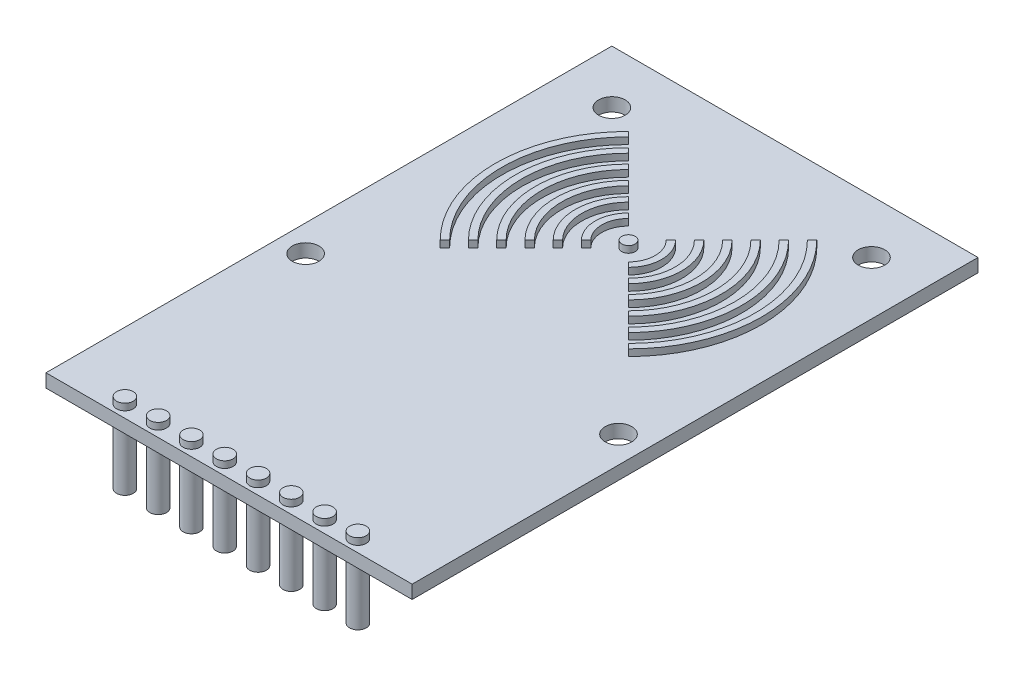
SolidWorks part; units mm, degrees
ref_plane "Plano frontal" through (0, 0, 0) normal (0, 0, 1) x (1, 0, 0)
ref_plane "Plano superior" through (0, 0, 0) normal (0, 1, 0) x (1, 0, 0)
ref_plane "Plano direito" through (0, 0, 0) normal (1, 0, 0) x (0, 0, -1)
sketch "Esboço1" plane through (0, 0, 0) normal (0, 1, 0) x (1, 0, 0)
  line L1 (-79.6852, 32.2564) -> (-24.6852, 32.2564)
  line L2 (-79.6852, 32.2564) -> (-79.6852, -52.7436)
  line L3 (-79.6852, -52.7436) -> (-24.6852, -52.7436)
  line L4 (-24.6852, 32.2564) -> (-24.6852, -52.7436)
  dimension "D1" = 85
  dimension "D2" = 55
extrude "Ressalto-extrusão1" add sketch "Esboço1" along normal blind 2
sketch "Esboço2" plane through (0, 2, 0) normal (0, 1, 0) x (1, 0, 0)
  line L0 (-24.6852, 32.2564) -> (-79.6852, 32.2564) construction
  line L1 (-79.6852, 32.2564) -> (-79.6852, -52.7436) construction
  line L2 (-24.6852, -52.7436) -> (-24.6852, 32.2564) construction
  line L3 (-66.3273, 21.3985) -> (-65.6202, 20.6914)
  line L4 (-77.1852, 32.2564) -> (-27.1852, 32.2564)
  line L5 (-77.1852, 32.2564) -> (-77.1852, -17.7436)
  line L6 (-77.1852, -17.7436) -> (-27.1852, -17.7436)
  line L7 (-27.1852, 32.2564) -> (-27.1852, -17.7436)
  line L8 (-66.3273, -6.8858) -> (-65.6202, -6.1787)
  line L9 (-27.1852, -17.7436) -> (-26.8918, -18.037)
  line L10 (-64.206, 19.2772) -> (-63.4989, 18.5701)
  line L11 (-62.0847, 17.1559) -> (-61.3776, 16.4488)
  line L12 (-59.9634, 15.0345) -> (-59.2563, 14.3274)
  line L13 (-57.842, 12.9132) -> (-57.1349, 12.2061)
  line L14 (-55.7207, 10.7919) -> (-55.0136, 10.0848)
  line L15 (-49.3568, 4.4279) -> (-48.6497, 3.7208)
  line L16 (-49.3568, 10.0848) -> (-48.6497, 10.7919)
  line L17 (-64.206, -4.7644) -> (-63.4989, -4.0573)
  line L18 (-62.0847, -2.6431) -> (-61.3776, -1.936)
  line L19 (-59.9634, -0.5218) -> (-59.2563, 0.1853)
  line L20 (-57.842, 1.5995) -> (-57.1349, 2.3066)
  line L21 (-55.7207, 3.7208) -> (-55.0136, 4.4279)
  line L22 (-47.2354, 2.3066) -> (-46.5283, 1.5995)
  line L23 (-47.2354, 12.2061) -> (-46.5283, 12.9132)
  line L24 (-45.1141, 14.3274) -> (-44.407, 15.0345)
  line L25 (-45.1141, 0.1853) -> (-44.407, -0.5218)
  line L26 (-42.9928, -1.936) -> (-42.2857, -2.6431)
  line L27 (-40.8715, -4.0573) -> (-40.1644, -4.7644)
  line L28 (-38.7502, -6.1787) -> (-38.0431, -6.8858)
  line L29 (-38.7502, 20.6914) -> (-38.0431, 21.3985)
  line L30 (-40.8715, 18.5701) -> (-40.1644, 19.2772)
  line L31 (-42.9928, 16.4488) -> (-42.2857, 17.1559)
  circle A0 centre (-52.1852, 7.2564) radius 1
  arc A1 (-55.0136, 10.0848) -> (-55.0136, 4.4279) centre (-52.1852, 7.2564) ccw
  arc A2 (-57.1349, 12.2061) -> (-57.1349, 2.3066) centre (-52.1852, 7.2564) ccw
  arc A3 (-59.2563, 14.3274) -> (-59.2563, 0.1853) centre (-52.1852, 7.2564) ccw
  arc A4 (-61.3776, 16.4488) -> (-61.3776, -1.936) centre (-52.1852, 7.2564) ccw
  arc A5 (-63.4989, 18.5701) -> (-63.4989, -4.0573) centre (-52.1852, 7.2564) ccw
  arc A6 (-65.6202, 20.6914) -> (-65.6202, -6.1787) centre (-52.1852, 7.2564) ccw
  arc A7 (-55.7207, 10.7919) -> (-55.7207, 3.7208) centre (-52.1852, 7.2564) ccw
  arc A8 (-57.842, 12.9132) -> (-57.842, 1.5995) centre (-52.1852, 7.2564) ccw
  arc A9 (-59.9634, 15.0345) -> (-59.9634, -0.5218) centre (-52.1852, 7.2564) ccw
  arc A10 (-62.0847, 17.1559) -> (-62.0847, -2.6431) centre (-52.1852, 7.2564) ccw
  arc A11 (-64.206, 19.2772) -> (-64.206, -4.7644) centre (-52.1852, 7.2564) ccw
  arc A12 (-66.3273, 21.3985) -> (-66.3273, -6.8858) centre (-52.1852, 7.2564) ccw
  circle A13 centre (-52.1852, 7.2564) radius 20 construction
  circle A14 centre (-52.1852, 7.2564) radius 19 construction
  circle A15 centre (-52.1852, 7.2564) radius 17 construction
  circle A16 centre (-52.1852, 7.2564) radius 16 construction
  circle A17 centre (-52.1852, 7.2564) radius 14 construction
  circle A18 centre (-52.1852, 7.2564) radius 13 construction
  circle A19 centre (-52.1852, 7.2564) radius 11 construction
  circle A20 centre (-52.1852, 7.2564) radius 10 construction
  circle A21 centre (-52.1852, 7.2564) radius 8 construction
  circle A22 centre (-52.1852, 7.2564) radius 7 construction
  circle A23 centre (-52.1852, 7.2564) radius 5 construction
  circle A24 centre (-52.1852, 7.2564) radius 4 construction
  arc A25 (-38.0431, -6.8858) -> (-38.0431, 21.3985) centre (-52.1852, 7.2564) ccw
  arc A26 (-38.7502, -6.1787) -> (-38.7502, 20.6914) centre (-52.1852, 7.2564) ccw
  arc A27 (-40.1644, -4.7644) -> (-40.1644, 19.2772) centre (-52.1852, 7.2564) ccw
  arc A28 (-40.8715, -4.0573) -> (-40.8715, 18.5701) centre (-52.1852, 7.2564) ccw
  arc A29 (-42.2857, -2.6431) -> (-42.2857, 17.1559) centre (-52.1852, 7.2564) ccw
  arc A30 (-42.9928, -1.936) -> (-42.9928, 16.4488) centre (-52.1852, 7.2564) ccw
  arc A31 (-44.407, -0.5218) -> (-44.407, 15.0345) centre (-52.1852, 7.2564) ccw
  arc A32 (-45.1141, 0.1853) -> (-45.1141, 14.3274) centre (-52.1852, 7.2564) ccw
  arc A33 (-46.5283, 1.5995) -> (-46.5283, 12.9132) centre (-52.1852, 7.2564) ccw
  arc A34 (-47.2354, 2.3066) -> (-47.2354, 12.2061) centre (-52.1852, 7.2564) ccw
  arc A35 (-48.6497, 3.7208) -> (-48.6497, 10.7919) centre (-52.1852, 7.2564) ccw
  arc A36 (-49.3568, 4.4279) -> (-49.3568, 10.0848) centre (-52.1852, 7.2564) ccw
  point P4 (-52.1852, 32.2564)
  dimension "D1" = 2
  dimension "D2" = 25
  dimension "D3" = 27.5
  dimension "D4" = 27.5
  dimension "D17" = 50
  dimension "D18" = 25
  dimension "D19" = 50
  dimension "D20" = 25
  dimension "D5" = 3
  dimension "D6" = 3
  dimension "D7" = 3
  dimension "D8" = 3
  dimension "D9" = 3
  dimension "D10" = 3
  dimension "D11" = 1
  dimension "D12" = 1
  dimension "D13" = 1
  dimension "D14" = 1
  dimension "D15" = 1
  dimension "D16" = 1
extrude "Ressalto-extrusão2" add sketch "Esboço2" along normal blind 1 contours A0 | L14 A7 L21 A1 | L13 A8 L20 A2 | L12 A9 L19 A3 | L11 A10 L18 A4 | L10 A11 L17 A5 | L3 A12 L8 A6 | A36 L15 A35 L16 | A34 L22 A33 L23 | A32 L25 A31 L24 | A30 L26 A29 L31 | A28 L27 A27 L30 | A26 L28 A25 L29
sketch "Esboço3" plane through (0, 2, 0) normal (0, 1, 0) x (1, 0, 0)
  line L0 (-79.6852, -52.7436) -> (-24.6852, -52.7436) construction
  line L1 (-72.6852, -52.7436) -> (-31.6852, -52.7436)
  line L2 (-72.6852, -52.7436) -> (-72.6852, -48.6992)
  line L3 (-72.6852, -48.6992) -> (-31.6852, -48.6992)
  line L4 (-31.6852, -52.7436) -> (-31.6852, -48.6992)
  line L5 (-79.6852, 32.2564) -> (-79.6852, -52.7436) construction
  line L6 (-24.6852, -52.7436) -> (-24.6852, 32.2564) construction
  circle A0 centre (-69.6852, -50.8911) radius 1.25
  circle A1 centre (-64.6852, -50.8911) radius 1.25
  circle A2 centre (-59.6852, -50.8911) radius 1.25
  circle A3 centre (-54.6852, -50.8911) radius 1.25
  circle A4 centre (-49.6852, -50.8911) radius 1.25
  circle A5 centre (-44.6852, -50.8911) radius 1.25
  circle A6 centre (-39.6852, -50.8911) radius 1.25
  circle A7 centre (-34.6852, -50.8911) radius 1.25
  dimension "D4" = 2.5
  dimension "D6" = 3
  dimension "D7" = 3
  dimension "D1" = 7
  dimension "D2" = 7
  dimension "D3" = 41
  dimension "D5" = 8
extrude "Ressalto-extrusão3" add sketch "Esboço3" along normal blind 1 and the other way blind 11 contours A7 | A6 | A5 | A4 | A3 | A2 | A1 | A0
sketch "Esboço4" plane through (0, 2, 0) normal (0, 1, 0) x (1, 0, 0)
  line L0 (-79.6852, 32.2564) -> (-79.6852, -52.7436) construction
  line L1 (-24.6852, -52.7436) -> (-24.6852, 32.2564) construction
  line L2 (-24.6852, 32.2564) -> (-79.6852, 32.2564) construction
  circle A0 centre (-71.6852, 24.2564) radius 2
  circle A1 centre (-32.6852, 24.2564) radius 2
  circle A2 centre (-75.6852, -17.7436) radius 2
  circle A3 centre (-28.6852, -17.7436) radius 2
  point P14 (-27.2281, 27.9152)
  dimension "D1" = 4
  dimension "D2" = 4
  dimension "D3" = 4
  dimension "D4" = 4
  dimension "D12" = 50
  dimension "D5" = 8
  dimension "D6" = 8
  dimension "D7" = 8
  dimension "D8" = 8
  dimension "D9" = 4
  dimension "D10" = 4
  dimension "D11" = 50
  dimension "D13" = 47
  dimension "D14" = 50
extrude "Corte-extrusão1" cut sketch "Esboço4" against normal blind 3
